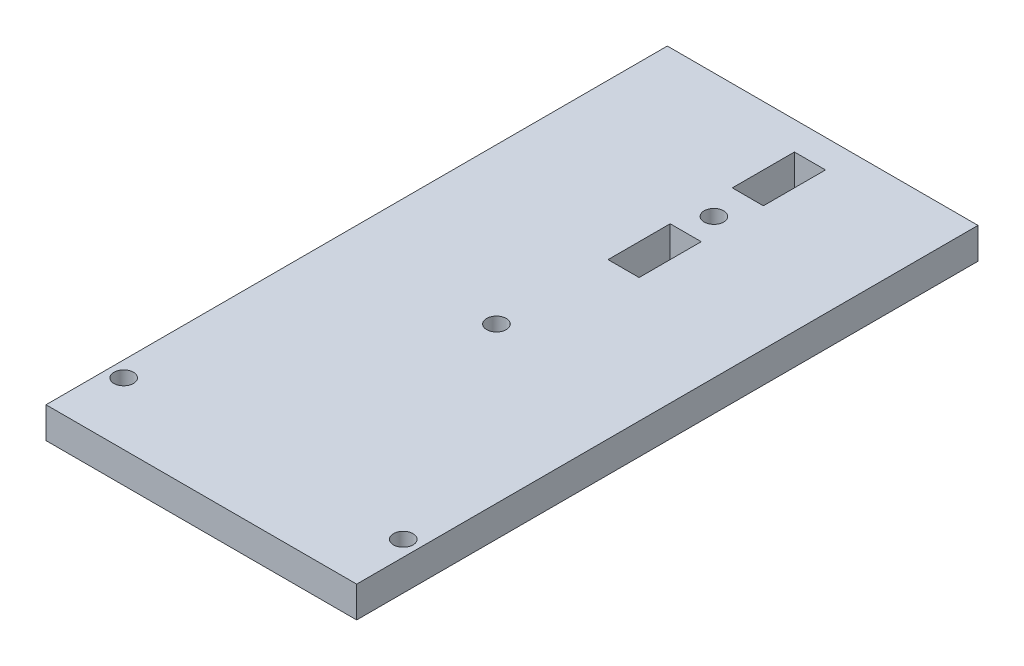
SolidWorks part; units mm, degrees
ref_plane "Front Plane" through (0, 0, 0) normal (0, 0, 1) x (1, 0, 0)
ref_plane "Top Plane" through (0, 0, 0) normal (0, 1, 0) x (1, 0, 0)
ref_plane "Right Plane" through (0, 0, 0) normal (1, 0, 0) x (0, 0, -1)
sketch "Sketch1" plane through (0, 0, 0) normal (0, 1, 0) x (1, 0, 0)
  line L1 (0, 0) -> (63.5, 0)
  line L2 (0, 0) -> (0, 127)
  line L3 (0, 127) -> (63.5, 127)
  line L4 (63.5, 0) -> (63.5, 127)
  circle A0 centre (3.175, 12.7) radius 2
  circle A1 centre (60.325, 12.7) radius 2
  circle A2 centre (31.75, 60.325) radius 2
  dimension "D3" = 4
  dimension "D4" = 4
  dimension "D5" = 4
  dimension "D7" = 3.175
  dimension "D8" = 31.75
  dimension "D9" = 47.625
  dimension "D10" = 12.7
  dimension "D1" = 63.5
  dimension "D2" = 127
  dimension "D6" = 3.175
  dimension "D11" = 12.7
extrude "Boss-Extrude1" add sketch "Sketch1" along normal blind 6.35
sketch "Sketch2" plane through (0, 6.35, 0) normal (0, 1, 0) x (1, 0, 0)
  line L1 (31.75, 95.83) -> (38.1, 95.83)
  line L2 (31.75, 95.83) -> (31.75, 83.13)
  line L3 (31.75, 83.13) -> (38.1, 83.13)
  line L4 (38.1, 95.83) -> (38.1, 83.13)
  line L5 (31.75, 108.53) -> (38.1, 108.53)
  line L6 (31.75, 108.53) -> (31.75, 121.23)
  line L7 (31.75, 121.23) -> (38.1, 121.23)
  line L8 (38.1, 108.53) -> (38.1, 121.23)
  circle A0 centre (34.925, 101.6) radius 2
  circle A1 centre (31.75, 60.325) radius 2 construction
  dimension "D1" = 41.275
  dimension "D3" = 4
  dimension "D9" = 12.7
  dimension "D2" = 3.175
  dimension "D4" = 3.175
  dimension "D5" = 6.35
  dimension "D6" = 6.35
  dimension "D7" = 3.175
  dimension "D8" = 12.7
  dimension "D10" = 12.7
extrude "Cut-Extrude1" cut sketch "Sketch2" against normal blind 6.35
